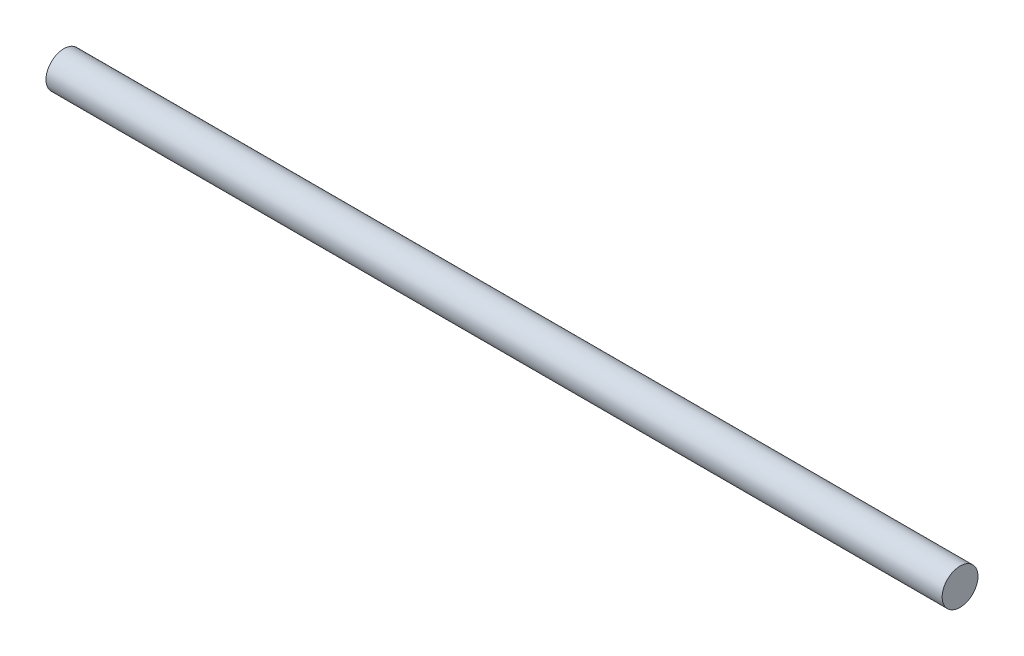
SolidWorks part; units mm, degrees
ref_plane "Front" through (0, 0, 0) normal (0, 0, 1) x (1, 0, 0)
ref_plane "Top" through (0, 0, 0) normal (0, 1, 0) x (1, 0, 0)
ref_plane "Right" through (0, 0, 0) normal (1, 0, 0) x (0, 0, -1)
sketch "Sketch1" plane through (0, 0, 0) normal (1, 0, 0) x (0, 0, -1)
  circle A0 centre (0, 0) radius 1.5875
  dimension "D1" = 3.175
extrude "Boss-Extrude1" add sketch "Sketch1" along normal mid plane 79.375
